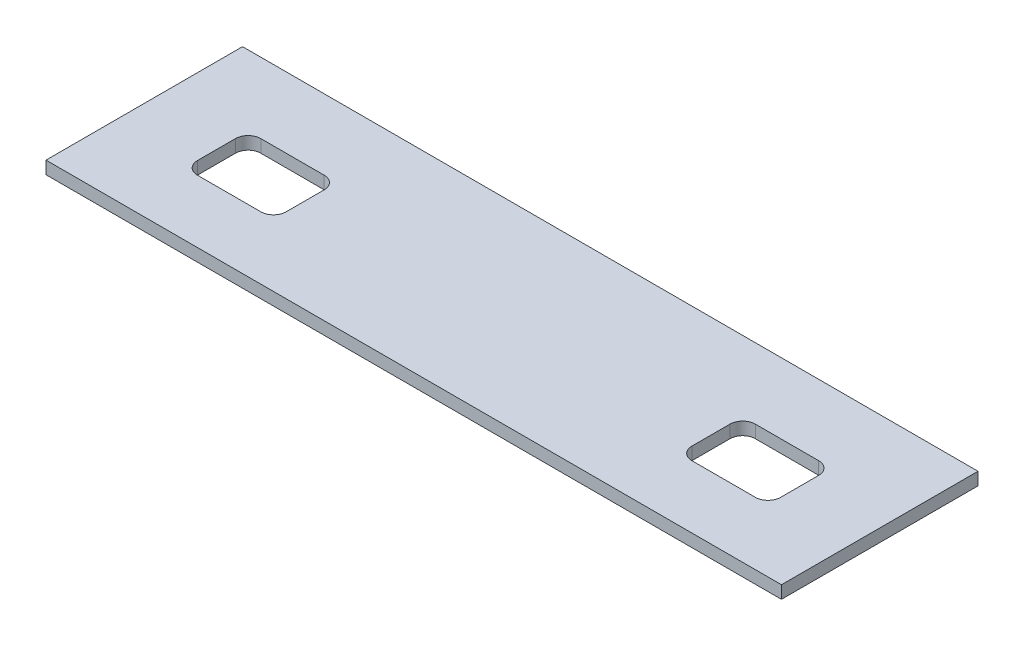
SolidWorks part; units mm, degrees
ref_plane "Plan de face" through (0, 0, 0) normal (0, 0, 1) x (1, 0, 0)
ref_plane "Plan de dessus" through (0, 0, 0) normal (0, 1, 0) x (1, 0, 0)
ref_plane "Plan de droite" through (0, 0, 0) normal (1, 0, 0) x (0, 0, -1)
sketch "Esquisse1" plane through (0, 0, 0) normal (0, 1, 0) x (1, 0, 0)
  line L1 (0, 0) -> (580, 0)
  line L2 (0, 0) -> (0, 155)
  line L3 (0, 155) -> (580, 155)
  line L4 (580, 0) -> (580, 155)
  dimension "D1" = 580
  dimension "D2" = 155
extrude "Boss.-Extru.1" add sketch "Esquisse1" along normal blind 10
sketch "Esquisse2" plane through (0, 10, 0) normal (0, 1, 0) x (1, 0, 0)
  line L0 (70, 99.4059) -> (70, 49.4059) construction
  line L1 (70, 99.4059) -> (120, 99.4059)
  line L2 (60, 89.4059) -> (60, 59.4059)
  line L3 (70, 49.4059) -> (120, 49.4059)
  line L4 (130, 89.4059) -> (130, 59.4059)
  line L5 (460, 99.4059) -> (510, 99.4059)
  line L6 (450, 89.4059) -> (450, 59.4059)
  line L7 (460, 49.4059) -> (510, 49.4059)
  line L8 (520, 89.4059) -> (520, 59.4059)
  line L9 (460, 99.4059) -> (460, 49.4059) construction
  line L14 (70, 49.4059) -> (120, 49.4059) construction
  arc A0 (510, 99.4059) -> (520, 89.4059) centre (510, 89.4059) cw
  arc A1 (520, 59.4059) -> (510, 49.4059) centre (510, 59.4059) cw
  arc A2 (460, 49.4059) -> (450, 59.4059) centre (460, 59.4059) cw
  arc A3 (450, 89.4059) -> (460, 99.4059) centre (460, 89.4059) cw
  arc A4 (120, 99.4059) -> (130, 89.4059) centre (120, 89.4059) cw
  arc A5 (130, 59.4059) -> (120, 49.4059) centre (120, 59.4059) cw
  arc A6 (70, 49.4059) -> (60, 59.4059) centre (70, 59.4059) cw
  arc A7 (60, 89.4059) -> (70, 99.4059) centre (70, 89.4059) cw
  point P17 (520, 99.4059)
  point P22 (450, 49.4059)
  point P25 (450, 99.4059)
  point P32 (60, 49.4059)
  point P35 (60, 99.4059)
  dimension "D8" = 10
  dimension "D1" = 50
  dimension "D2" = 70
  dimension "D3" = 10
  dimension "D4" = 70
  dimension "D5" = 10
  dimension "D6" = 50
  dimension "D7" = 0
extrude "Enlèv. mat.-Extru.1" cut sketch "Esquisse2" against normal blind 10
